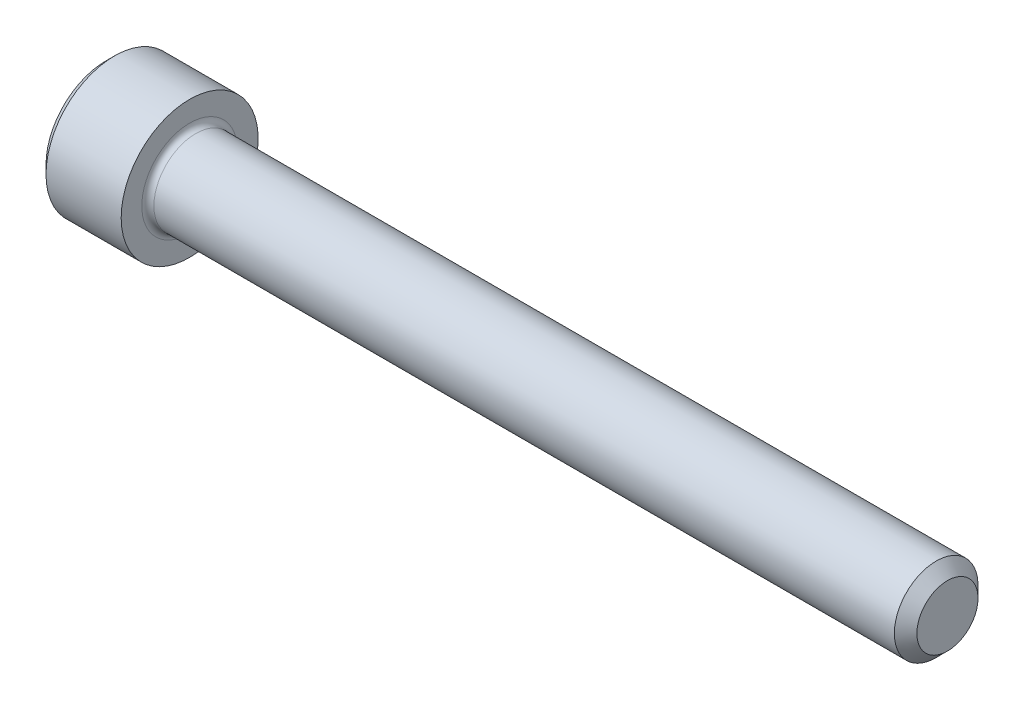
SolidWorks part; units mm, degrees
ref_plane "Plane1" through (0, 0, 0) normal (0, 0, 1) x (1, 0, 0)
ref_plane "Plane2" through (0, 0, 0) normal (0, 1, 0) x (1, 0, 0)
ref_plane "Plane3" through (0, 0, 0) normal (1, 0, 0) x (0, 0, -1)
sketch "BodySke" plane through (0, 0, 0) normal (0, 0, 1) x (1, 0, 0)
  line L0 (0, 0) -> (0, 2.5146)
  line L1 (0.3556, 2.8702) -> (3.5052, 2.8702)
  line L2 (3.5052, 2.8702) -> (3.5052, 1.7526)
  line L3 (3.5052, 1.7526) -> (34.7828, 1.7526)
  line L4 (35.2552, 1.2802) -> (35.2552, 0)
  line L5 (35.2552, 0) -> (0, 0)
  line L6 (-31.75, 0) -> (127, 0) construction
  line L7 (0, 2.5146) -> (0.3556, 2.8702)
  line L8 (35.2552, 1.2802) -> (34.7828, 1.7526)
  line L9 (0, -2.5146) -> (0.3556, -2.8702) construction
  line L10 (35.2552, -1.2802) -> (34.7828, -1.7526) construction
  line L11 (4.2977, 9.525) -> (4.2977, 3.175) construction
  line L12 (16.2052, 9.525) -> (16.2052, 3.175) construction
  line L13 (-2.8448, 9.525) -> (-2.8448, 3.175) construction
  dimension "Diameter" = 3.5052
  dimension "Head_ht" = 3.5052
  dimension "Length" = 31.75
  dimension "Body_ch_ang" = 45
  dimension "Head_dia" = 5.7404
  dimension "Head_ch_ang" = 45
  dimension "Head_side_ht" = 3.1496
  dimension "Minor_dia" = 2.5603
  dimension "Advance" = 0.7925
  dimension "Thread_nom" = 19.05
  dimension "Thread_length" = 38.1
revolve "Base-Revolve" add sketch "BodySke"
cosmetic thread "ThreadCosmetic"
fillet "Fillet1" radius 0.254 1 edges at (3.5052, 0, 1.7526)
sketch "Sketch2" plane through (0, 0, 0) normal (0, 0, 1) x (1, 0, 0)
  line L0 (0, 1.3843) -> (1.6256, 1.3843)
  line L1 (1.6256, 1.3843) -> (2.4248, 0)
  line L2 (-31.75, 0) -> (127, 0) construction
  line L3 (2.4248, 0) -> (0, 0)
  line L4 (0, 0) -> (0, 1.3843)
  line L5 (0, 2.5146) -> (0, -2.5146) construction
  line L6 (0, 0) -> (47.625, 0) construction
  line L7 (3.5052, -2.8702) -> (3.5052, 2.8702) construction
  dimension "D1" = 1.3843
  dimension "D2" = 60
  dimension "Wall_thickness" = 1.8796
revolve "Hex-PreBroach" cut sketch "Sketch2" angle 360 about L6
sketch "Sketch3" plane through (0, 0, 0) normal (-1, 0, 0) x (0, 0.5, 0.866)
  line L0 (0.7992, 1.3843) -> (-0.7992, 1.3843)
  line L1 (-0.7992, 1.3843) -> (-1.5985, 0)
  line L2 (0.7992, 1.3843) -> (1.5985, 0)
  line L3 (0.7992, -1.3843) -> (1.5985, 0)
  line L4 (0.7992, -1.3843) -> (-0.7992, -1.3843)
  line L5 (-0.7992, -1.3843) -> (-1.5985, 0)
  dimension "D1" = 1.3843
  dimension "D2" = 1.3843
  dimension "Hex_size" = 2.7686
extrude "Hex" cut sketch "Sketch3" against normal blind 1.6256
sketch "Sketch4" plane through (0, 0, 0) normal (-1, 0, 0) x (0, 0, 1)
  line L0 (0, 0) -> (1.7399, 0)
  line L1 (0, 0) -> (6.1484, 3.5498) construction
  line L2 (0, 0) -> (0.8699, 1.5068)
  line L3 (1.4457, 0.3947) -> (1.6607, 0.5189)
  line L4 (1.0647, 1.0546) -> (1.2797, 1.1788)
  arc A0 (1.4457, 0.3947) -> (1.0647, 1.0546) centre (0, 0) ccw
  arc A1 (1.7399, 0) -> (1.6607, 0.5189) centre (0, 0) ccw
  arc A2 (0.8699, 1.5068) -> (1.2797, 1.1788) centre (0, 0) cw
  dimension "D1" = 30
  dimension "Spline_n_dim" = 2.9972
  dimension "Spline_m_dim" = 3.4798
  dimension "D2" = 60
  dimension "D3" = 0.381
  dimension "Spline_p_dim" = 0.762
extrude "Spline" [suppressed] cut sketch "Sketch4" against normal blind 1.6256
pattern_circular "CirPattern1" [suppressed] count 6 every 60
sketch "Sketch5" plane through (0, 0, 0) normal (0, 0, 1) x (1, 0, 0)
  line L0 (-31.75, 0) -> (127, 0) construction
  line L2 (0, 2.5146) -> (0, -2.5146) construction
  circle A0 centre (1.27, 0) radius 0.4445
  dimension "Drilled_hole_dia" = 0.889
  dimension "Drilled_hole_loc" = 1.27
extrude "Hole" [suppressed] cut sketch "Sketch5" against normal through all and the other way through all
pattern_circular "Drilled-4" [suppressed] count 2 every 60
pattern_circular "Drilled-6" [suppressed] count 3 every 60
sketch "ThdSchSke" plane through (0, 0, 0) normal (0, 0, 1) x (1, 0, 0)
  line L0 (16.2052, -1.2802) -> (15.8744, -1.7526)
  line L1 (16.2052, -1.2802) -> (16.536, -1.7526)
  line L2 (16.536, -1.7526) -> (16.536, -2.1908)
  line L3 (-3.175, 0) -> (5.1513, 0) construction
  line L5 (16.536, -2.1908) -> (15.8744, -2.1908)
  line L6 (15.8744, -2.1908) -> (15.8744, -1.7526)
  line L7 (0, 2.5146) -> (0, -2.5146) construction
  dimension "Thread_minor" = 2.5603
  dimension "Diameter" = 3.5052
  dimension "Start" = 16.2052
  dimension "SideAngle" = 55
  dimension "VeeAngle" = 70
  dimension "Overcut" = 4.3815
revolve "ThreadSchematic" [suppressed] cut sketch "ThdSchSke" angle 360 about L3
pattern_linear "ThdSchPat" [suppressed]
equation "\"D2@Sketch3\" = \"Hex_size@Sketch3\" / 2"
equation "\"D1@Sketch3\" = \"Hex_size@Sketch3\" / 2"
equation "\"D1@Sketch2\" = \"Hex_size@Sketch3\" / 2"
equation "\"D3@Sketch4\" = \"Spline_p_dim@Sketch4\" / 2"
equation "\"Thread_minor@ThreadCosmetic\"  =  \"Minor_dia@BodySke\""
equation "\"D2@CirPattern1\" = 360 / \"Num_teeth@CirPattern1\""
equation "\"Wall_thickness@Sketch2\" = \"Head_ht@BodySke\" - \"Key_eng@Hex\""
equation "\"Thread_length@ThreadCosmetic\" = ((sgn( (\"Length@BodySke\" - \"Advance@BodySke\" ) - \"Thread_nom@BodySke\" )-1)*( (\"Length@BodySke\" - \"Advance@BodySke\" ) - \"Thread_nom@BodySke\" ))/-2+ \"Thread_nom@BodySke\""
equation "\"Thread_minor@ThdSchSke\" = \"Minor_dia@BodySke\""
equation "\"Diameter@ThdSchSke\" = \"Diameter@BodySke\""
equation "\"Overcut@ThdSchSke\" = \"Diameter@BodySke\" * 1.25"
equation "\"Start@ThdSchSke\" = \"Head_ht@BodySke\" + \"Length@BodySke\" - \"Thread_length@ThreadCosmetic\"  '---Non-countersunk---"
equation "\"Num_threads@ThdSchPat\" = int( \"Thread_length@ThreadCosmetic\" / \"Advance@BodySke\" + 0.999 )  + 1"
equation "\"Advance@ThdSchPat\" = \"Thread_length@ThreadCosmetic\" /  (\"Num_threads@ThdSchPat\" - 1) 'relax it"
equation "\"Num_threads@ThdSchPat\" = \"Num_threads@ThdSchPat\" - sgn( \"Num_threads@ThdSchPat\" - 1) '---chamfered tips only---"
